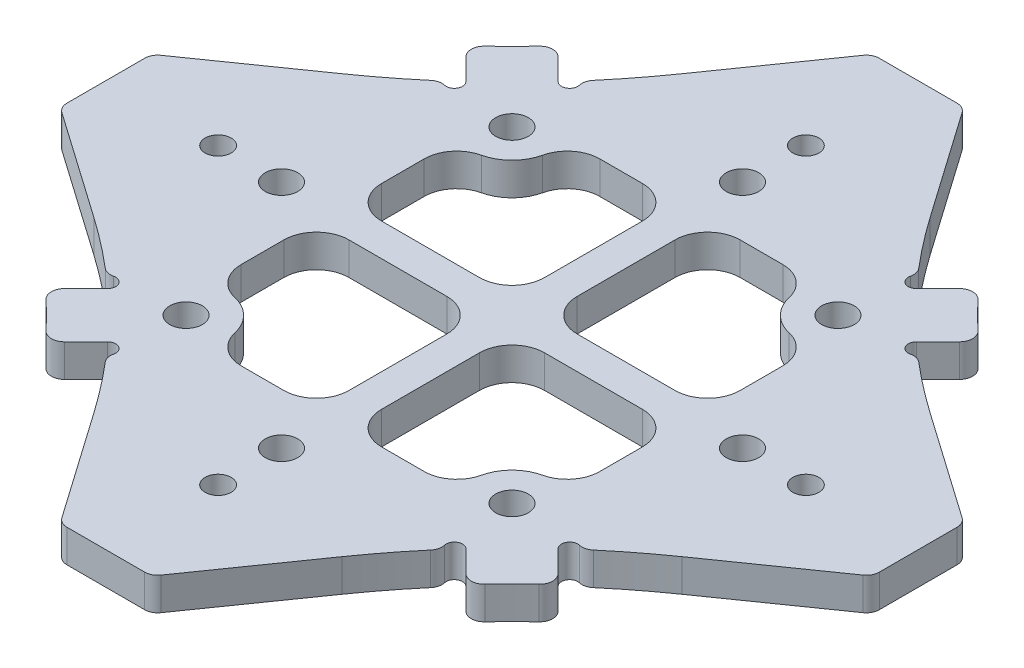
SolidWorks part; units mm, degrees
ref_plane "前视基准面" through (0, 0, 0) normal (0, 0, 1) x (1, 0, 0)
ref_plane "上视基准面" through (0, 0, 0) normal (0, 1, 0) x (1, 0, 0)
ref_plane "右视基准面" through (0, 0, 0) normal (1, 0, 0) x (0, 0, -1)
sketch "草图1" plane through (0, 0, 0) normal (0, 1, 0) x (1, 0, 0)
  line L13 (7.6123, 18.0495) -> (2.8008, 24.921)
  line L70 (0, 24.921) -> (0, 18.8312)
  line L96 (0, 0) -> (1, 1)
  line L101 (14.2836, 14.2836) -> (10.7071, 10.7071)
  line L104 (0, 24.921) -> (2.8008, 24.921)
  line L107 (10.2863, 14.5289) -> (10.328, 14.5706)
  line L110 (1, 1) -> (1, 11)
  line L113 (10.9934, 13.8218) -> (12.9049, 15.7333)
  line L120 (1, 11) -> (7.7087, 11)
  line L128 (9.2929, 9.2929) -> (8.2322, 8.2322)
  line L129 (0, 13.1421) -> (0, 0)
  line L130 (0, 17.2312) -> (0, 15.1421)
  arc A119 (7.6123, 18.0495) -> (10.328, 14.5706) centre (42.427, 42.427) ccw
  arc A121 (14.2836, 14.2836) -> (12.9049, 15.7333) centre (42.4264, 42.4264) cw
  arc A122 (0, 17.2312) -> (0, 18.8312) centre (0, 18.0312) ccw
  arc A126 (10.9934, 13.8218) -> (10.2863, 14.5289) centre (10.6398, 14.1754) cw
  arc A129 (0, 13.1421) -> (0, 15.1421) centre (0, 14.1421) ccw
  arc A130 (10.7071, 10.7071) -> (9.2929, 9.2929) centre (10, 10) ccw
  arc A131 (7.7087, 11) -> (8.2322, 8.2322) centre (10, 10) ccw
extrude "凸台-拉伸1" add sketch "草图1" along normal blind 2
mirror "镜向1" about plane through (0, 2, 0) normal (0.7071, 0, 0.7071) of "凸台-拉伸1"
mirror "镜向2" about plane through (0, 2, 0) normal (1, 0, 0) of bodies 123
mirror "镜向3" about plane through (0, 2, 0) normal (0, 0, 1) of bodies 124
fillet "圆角1" radius 0.8 24 edges at (14.5706, 1, 10.328) (15.7333, 1, 12.9049) (10.328, 1, 14.5706) (2.8008, 1, 24.921) (-2.8008, 1, 24.921) (-10.328, 1, 14.5706) (-12.9049, 1, 15.7333) (-15.7333, 1, 12.9049) (-14.5706, 1, 10.328) (-24.921, 1, 2.8008) (-24.921, 1, -2.8008) (-14.5706, 1, -10.328) (-15.7333, 1, -12.9049) (-12.9049, 1, -15.7333) (-10.328, 1, -14.5706) (-2.8008, 1, -24.921) (2.8008, 1, -24.921) (10.328, 1, -14.5706) (12.9049, 1, -15.7333) (15.7333, 1, -12.9049) (14.5706, 1, -10.328) (24.921, 1, -2.8008) (24.921, 1, 2.8008) (12.9049, 1, 15.7333)
fillet "圆角2" radius 2 20 edges at (-11, 1, 1) (-11, 1, 7.7087) (-7.7087, 1, 11) (-1, 1, 11) (-1, 1, 1) (1, 1, 1) (1, 1, 11) (7.7087, 1, 11) (11, 1, 7.7087) (11, 1, 1) (-1, 1, -1) (-1, 1, -11) (-7.7087, 1, -11) (-11, 1, -7.7087) (-11, 1, -1) (11, 1, -1) (11, 1, -7.7087) (7.7087, 1, -11) (1, 1, -1) (1, 1, -11)
